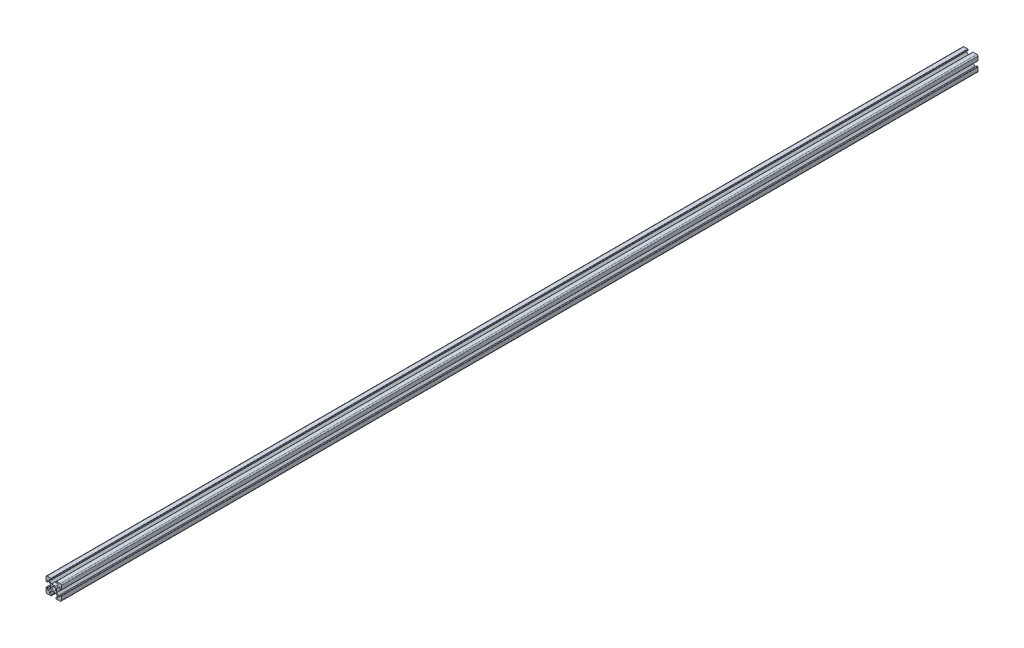
SolidWorks part; units mm, degrees
ref_plane "前视基准面" through (0, 0, 0) normal (0, 0, 1) x (1, 0, 0)
ref_plane "上视基准面" through (0, 0, 0) normal (0, 1, 0) x (1, 0, 0)
ref_plane "右视基准面" through (0, 0, 0) normal (1, 0, 0) x (0, 0, -1)
sketch "草图1" plane through (0, 0, 0) normal (0, 0, 1) x (1, 0, 0)
  line L0 (0, 6.9) -> (0, 0)
  line L1 (20, 20) -> (20, 13.1)
  line L2 (1.8, 15.5) -> (3.2272, 15.5)
  line L3 (4.5, 16.7728) -> (4.5, 18.2)
  line L4 (0, 13.1) -> (0, 20)
  line L5 (6.9, 20) -> (6.9, 18.2)
  line L6 (6.9, 18.2) -> (4.5, 18.2)
  line L7 (13.1, 20) -> (20, 20)
  line L8 (6.9, 20) -> (0, 20)
  line L9 (0, 0) -> (6.9, 0)
  line L10 (13.1, 0) -> (20, 0)
  line L11 (15.5, 18.2) -> (15.5, 16.7728)
  line L12 (16.7728, 15.5) -> (18.2, 15.5)
  line L13 (20, 6.9) -> (20, 0)
  line L14 (1.8, 4.5) -> (3.2272, 4.5)
  line L15 (4.5, 3.2272) -> (4.5, 1.8)
  line L16 (12.6272, 6.1) -> (15.5, 3.2272)
  line L17 (18.2, 4.5) -> (16.7728, 4.5)
  line L18 (15.5, 3.2272) -> (15.5, 1.8)
  line L19 (13.9, 7.3728) -> (16.7728, 4.5)
  line L20 (13.1, 20) -> (13.1, 18.2)
  line L21 (13.1, 18.2) -> (15.5, 18.2)
  line L22 (7.3728, 13.9) -> (12.6272, 13.9)
  line L23 (13.9, 12.6272) -> (13.9, 7.3728)
  line L24 (7.3728, 6.1) -> (12.6272, 6.1)
  line L25 (6.1, 12.6272) -> (6.1, 7.3728)
  line L27 (12.6272, 13.9) -> (15.5, 16.7728)
  line L30 (3.2272, 4.5) -> (6.1, 7.3728)
  line L32 (4.5, 3.2272) -> (7.3728, 6.1)
  line L33 (20, 13.1) -> (18.2, 13.1)
  line L34 (18.2, 13.1) -> (18.2, 15.5)
  line L36 (20, 6.9) -> (18.2, 6.9)
  line L37 (18.2, 6.9) -> (18.2, 4.5)
  line L39 (13.1, 0) -> (13.1, 1.8)
  line L40 (13.1, 1.8) -> (15.5, 1.8)
  line L42 (6.9, 0) -> (6.9, 1.8)
  line L43 (6.9, 1.8) -> (4.5, 1.8)
  line L45 (0, 6.9) -> (1.8, 6.9)
  line L46 (1.8, 6.9) -> (1.8, 4.5)
  line L48 (0, 13.1) -> (1.8, 13.1)
  line L49 (1.8, 13.1) -> (1.8, 15.5)
  line L50 (4.5, 16.7728) -> (7.3728, 13.9)
  line L51 (3.2272, 15.5) -> (6.1, 12.6272)
  line L53 (13.9, 12.6272) -> (16.7728, 15.5)
  line L62 (1.8, 13.1) -> (1.8, 15.5)
  line L63 (0, 13.1) -> (1.8, 13.1)
  line L66 (6.9, 18.2) -> (4.5, 18.2)
  line L67 (6.9, 20) -> (6.9, 18.2)
  line L68 (3.2272, 15.5) -> (1.8, 15.5)
  line L69 (4.5, 18.2) -> (4.5, 16.7728)
  line L75 (4.5, 1.8) -> (4.5, 3.2272)
  line L76 (3.2272, 4.5) -> (1.8, 4.5)
  line L77 (6.9, 0) -> (6.9, 1.8)
  line L78 (6.9, 1.8) -> (4.5, 1.8)
  line L80 (0, 6.9) -> (1.8, 6.9)
  line L81 (1.8, 6.9) -> (1.8, 4.5)
  line L90 (1.8, 6.9) -> (1.8, 4.5)
  line L91 (0, 6.9) -> (1.8, 6.9)
  line L93 (18.2, 6.9) -> (18.2, 4.5)
  line L94 (20, 6.9) -> (18.2, 6.9)
  line L98 (13.1, 1.8) -> (15.5, 1.8)
  line L99 (13.1, 0) -> (13.1, 1.8)
  line L100 (16.7728, 4.5) -> (18.2, 4.5)
  line L101 (15.5, 1.8) -> (15.5, 3.2272)
  line L106 (6.9, 1.8) -> (4.5, 1.8)
  line L107 (6.9, 0) -> (6.9, 1.8)
  line L109 (4.5, 3.2272) -> (4.5, 1.8)
  line L110 (1.8, 4.5) -> (3.2272, 4.5)
  circle A0 centre (10, 10) radius 2.5
extrude "凸台-拉伸1" add sketch "草图1" along normal blind 1200 contours L23 L53 L12 L34 L33 L1 L7 L20 L21 L11 L27 L22 L50 L3 L6 L5 L8 L4 L48 L49 L2 L51 L25 L30 L14 L46 L45 L0 L9 L42 L43 L15 L32 L24 L16 L18 L40 L39 L10 L13 L36 L37 L17 L19
fillet "圆角1" radius 1.5 1 edges at (20, 20, 600)
fillet "圆角2" radius 1.5 1 edges at (0, 20, 600)
fillet "圆角3" radius 1.5 1 edges at (0, 0, 600)
fillet "圆角4" radius 1.5 1 edges at (20, 0, 600)
fillet "圆角5" radius 0.5 1 edges at (13.1, 20, 600)
fillet "圆角6" radius 0.5 1 edges at (6.9, 20, 600)
fillet "圆角7" radius 0.5 1 edges at (0, 13.1, 600)
fillet "圆角8" radius 0.5 1 edges at (0, 6.9, 600)
fillet "圆角9" radius 0.5 1 edges at (6.9, 0, 600)
fillet "圆角10" radius 0.5 1 edges at (13.1, 0, 600)
fillet "圆角11" radius 0.5 1 edges at (20, 13.1, 600)
fillet "圆角12" radius 0.5 1 edges at (20, 6.9, 600)
